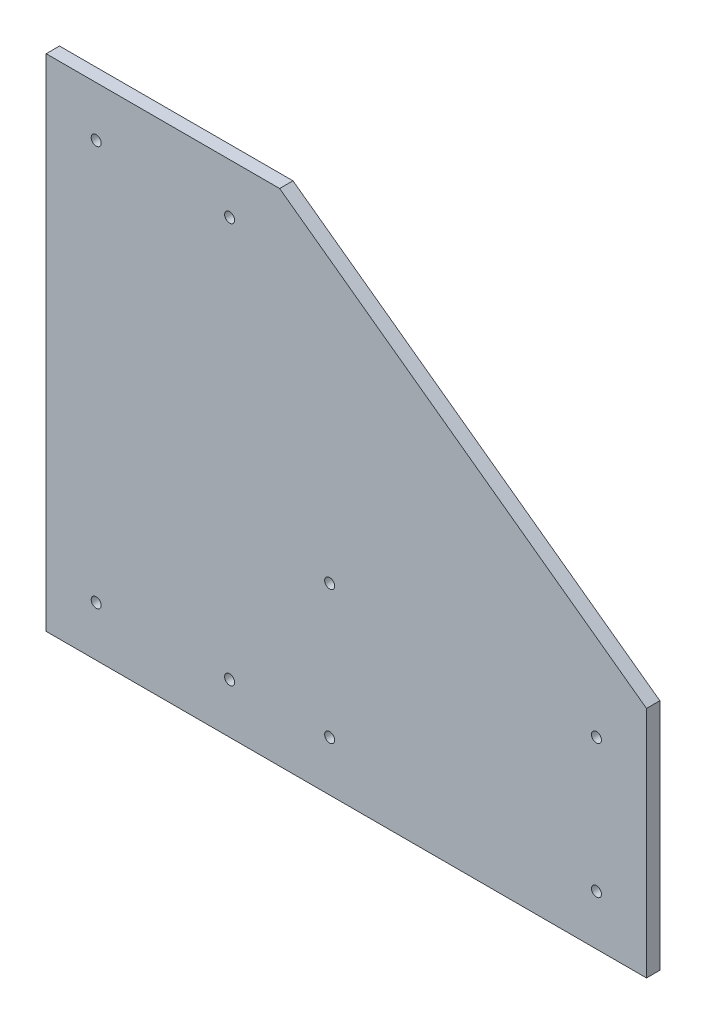
SolidWorks part; units mm, degrees
ref_plane "Front Plane" through (0, 0, 0) normal (0, 0, 1) x (1, 0, 0)
ref_plane "Top Plane" through (0, 0, 0) normal (0, 1, 0) x (1, 0, 0)
ref_plane "Right Plane" through (0, 0, 0) normal (1, 0, 0) x (0, 0, -1)
sketch "Sketch1" plane through (0, 0, 0) normal (0, 0, 1) x (1, 0, 0)
  line L0 (0, 0) -> (228.6, 0)
  line L1 (228.6, 0) -> (228.6, 88.9)
  line L2 (228.6, 88.9) -> (88.9, 190.5)
  line L3 (88.9, 190.5) -> (0, 190.5)
  line L4 (0, 190.5) -> (0, 0)
  dimension "D1" = 88.9
  dimension "D2" = 88.9
  dimension "D3" = 101.6
  dimension "D4" = 139.7
extrude "Boss-Extrude1" add sketch "Sketch1" along normal blind 5.08
hole_wizard "#6 Clearance Hole1" positions "Sketch2" profile "Sketch3" hole size "#6" standard "ANSI Inch" end condition through all
sketch "Sketch2" plane through (0, 0, 5.08) normal (0, 0, 1) x (1, 0, 0)
  line L3 (228.6, 0) -> (228.6, 88.9) construction
  line L7 (44.45, 190.5) -> (44.45, 0) construction
  line L8 (88.9, 190.5) -> (0, 190.5) construction
  line L9 (0, 0) -> (228.6, 0) construction
  line L12 (69.85, 171.45) -> (19.05, 171.45)
  line L13 (69.85, 171.45) -> (69.85, 19.05)
  line L14 (69.85, 19.05) -> (19.05, 19.05)
  line L15 (19.05, 171.45) -> (19.05, 19.05)
  line L16 (69.85, 171.45) -> (19.05, 19.05) construction
  line L17 (69.85, 19.05) -> (19.05, 171.45) construction
  line L18 (0, 190.5) -> (0, 0) construction
  line L19 (228.6, 44.45) -> (0, 44.45) construction
  line L22 (107.95, 19.05) -> (209.55, 19.05)
  line L23 (107.95, 19.05) -> (107.95, 69.85)
  line L24 (107.95, 69.85) -> (209.55, 69.85)
  line L25 (209.55, 19.05) -> (209.55, 69.85)
  line L26 (107.95, 19.05) -> (209.55, 69.85) construction
  line L27 (107.95, 69.85) -> (209.55, 19.05) construction
  point P81 (44.45, 95.25)
  point P115 (19.05, 171.45)
  point P118 (69.85, 171.45)
  point P121 (69.85, 19.05)
  point P124 (19.05, 19.05)
  point P127 (107.95, 19.05)
  point P130 (107.95, 69.85)
  point P133 (209.55, 69.85)
  point P136 (209.55, 19.05)
  point P138 (0, 0)
  point P139 (171.45, 91.7828)
  point P140 (158.75, 44.45)
  dimension "D1" = 19.05
  dimension "D2" = 19.05
  dimension "D3" = 19.05
  dimension "D4" = 19.05
  dimension "D5" = 19.05
sketch "Sketch3" plane through (209.55, 19.05, 5.08) normal (1, 0, 0) x (0, -1, 0)
  line L0 (0, 0) -> (0, 5.08)
  line L1 (0, 5.08) -> (1.8986, 5.08)
  line L2 (1.8986, 5.08) -> (1.8986, 0)
  line L5 (1.8986, 0) -> (0, 0)
  line L11 (0, -6.35) -> (0, 107.95) construction
  dimension "Thru Hole Dia." = 3.7973
  dimension "Thru Hole Depth" = 5.08
